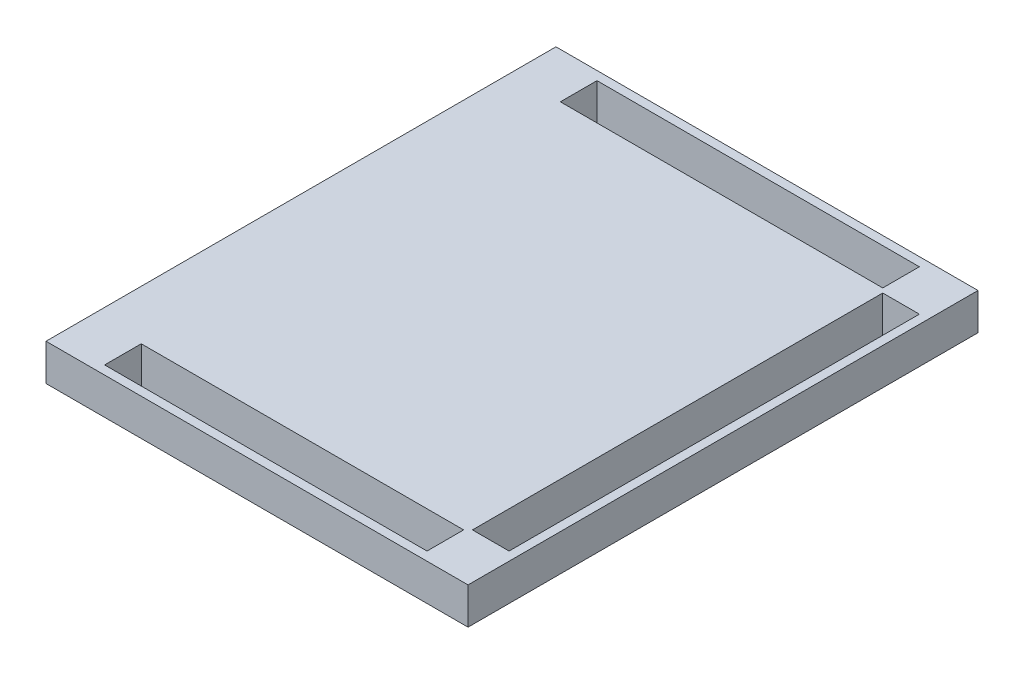
SolidWorks part; units mm, degrees
ref_plane "Front Plane" through (0, 0, 0) normal (0, 0, 1) x (1, 0, 0)
ref_plane "Top Plane" through (0, 0, 0) normal (0, 1, 0) x (1, 0, 0)
ref_plane "Right Plane" through (0, 0, 0) normal (1, 0, 0) x (0, 0, -1)
sketch "Sketch1" plane through (0, 0, 0) normal (0, 1, 0) x (1, 0, 0)
  line L1 (-32.2227, 333.0112) -> (255.7773, 333.0112)
  line L2 (-32.2227, 333.0112) -> (-32.2227, -14.9888)
  line L3 (-32.2227, -14.9888) -> (255.7773, -14.9888)
  line L4 (255.7773, 333.0112) -> (255.7773, -14.9888)
  dimension "D1" = 348
  dimension "D2" = 288
extrude "Boss-Extrude1" add sketch "Sketch1" along normal blind 25
sketch "Sketch2" plane through (0, 0, 0) normal (0, 1, 0) x (1, 0, 0)
  line L0 (-32.2227, -14.9888) -> (255.7773, -14.9888) construction
  line L2 (255.7773, -14.9888) -> (255.7773, 333.0112) construction
  line L3 (255.7773, 333.0112) -> (-32.2227, 333.0112) construction
  line L13 (1.7773, 327.0112) -> (221.7773, 327.0112)
  line L14 (1.7773, 327.0112) -> (1.7773, 302.0112)
  line L15 (1.7773, 302.0112) -> (221.7773, 302.0112)
  line L16 (221.7773, 327.0112) -> (221.7773, 302.0112)
  line L21 (1.7773, 16.0112) -> (221.7773, 16.0112)
  line L22 (1.7773, 16.0112) -> (1.7773, -8.9888)
  line L23 (1.7773, -8.9888) -> (221.7773, -8.9888)
  line L24 (221.7773, 16.0112) -> (221.7773, -8.9888)
  line L25 (224.7773, 299.0112) -> (249.7773, 299.0112)
  line L26 (224.7773, 299.0112) -> (224.7773, 19.0112)
  line L27 (224.7773, 19.0112) -> (249.7773, 19.0112)
  line L28 (249.7773, 299.0112) -> (249.7773, 19.0112)
  dimension "D2" = 220
  dimension "D3" = 220
  dimension "D4" = 34
  dimension "D5" = 6
  dimension "D6" = 34
  dimension "D7" = 25
  dimension "D8" = 34
  dimension "D10" = 25
  dimension "D11" = 25
  dimension "D12" = 6
extrude "Cut-Extrude5" cut sketch "Sketch2" along normal blind 25
